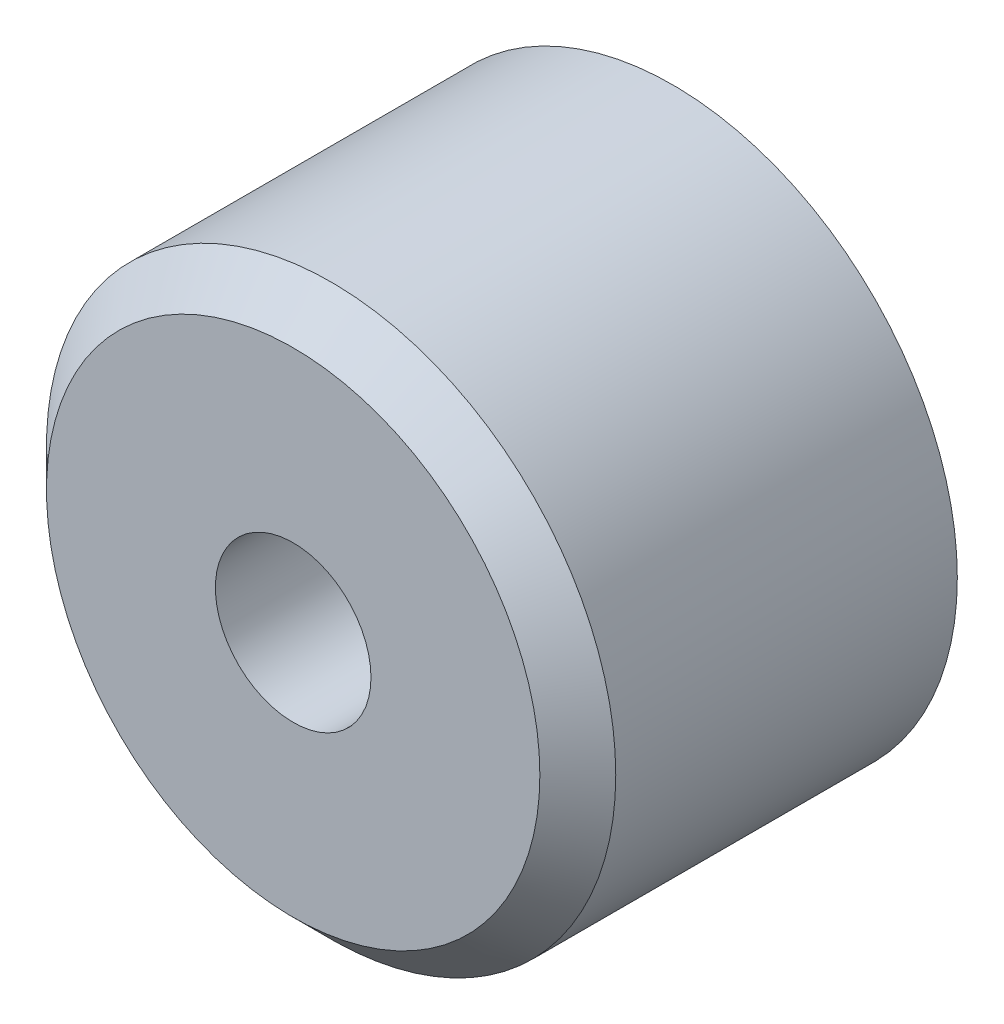
SolidWorks part; units mm, degrees
material "7075-T6 (SN)"
ref_plane "Plan de face" through (0, 0, 0) normal (0, 0, 1) x (1, 0, 0)
ref_plane "Plan de dessus" through (0, 0, 0) normal (0, 1, 0) x (1, 0, 0)
ref_plane "Plan de droite" through (0, 0, 0) normal (1, 0, 0) x (0, 0, -1)
sketch "Esquisse1" plane through (0, 0, 0) normal (0, 0, 1) x (1, 0, 0)
  circle A0 centre (0, 0) radius 7.5
  circle A1 centre (0, 0) radius 5.05
  dimension "D1" = 15
  dimension "D2" = 10.1
extrude "Boss.-Extru.1" add sketch "Esquisse1" along normal up to surface (1 mm away)
sketch "Esquisse2" plane through (0, 0, 1) normal (0, 0, 1) x (1, 0, 0)
  circle A0 centre (0, 0) radius 7.5
  circle A1 centre (0, 0) radius 2.05
  dimension "D1" = 4.1
extrude "Boss.-Extru.2" add sketch "Esquisse2" along normal blind 9
chamfer "Chanfrein1" distance 1 angle 45 1 edges at (7.5, 0, 10)
